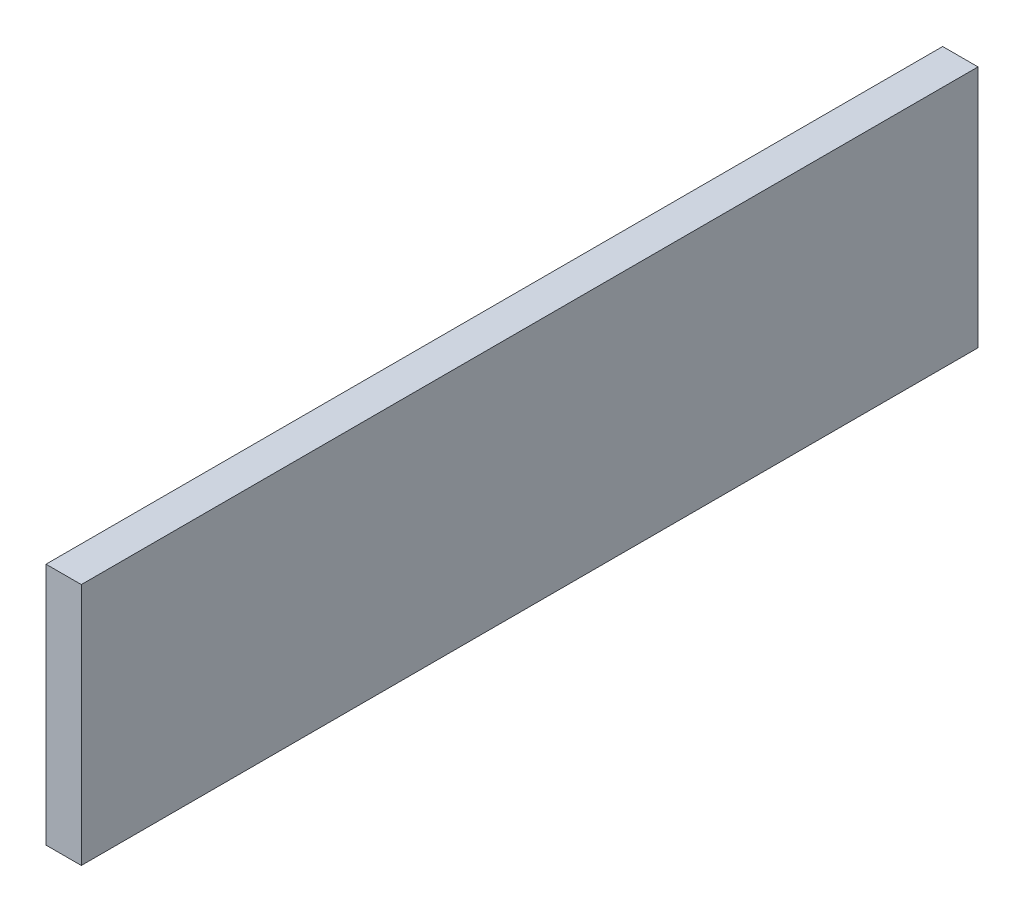
SolidWorks part; units mm, degrees
ref_plane "Спереди" through (0, 0, 0) normal (0, 0, 1) x (1, 0, 0)
ref_plane "Сверху" through (0, 0, 0) normal (0, 1, 0) x (1, 0, 0)
ref_plane "Справа" through (0, 0, 0) normal (1, 0, 0) x (0, 0, -1)
sketch "Эскиз1" plane through (0, 0, 0) normal (1, 0, 0) x (0, 0, -1)
  line L1 (411.3957, -20.2686) -> (-45.6043, -20.2686)
  line L2 (411.3957, -20.2686) -> (411.3957, 103.7314)
  line L3 (411.3957, 103.7314) -> (-45.6043, 103.7314)
  line L4 (-45.6043, -20.2686) -> (-45.6043, 103.7314)
  dimension "D1" = 124
  dimension "D2" = 457
extrude "Бобышка-Вытянуть1" add sketch "Эскиз1" along normal blind 18
